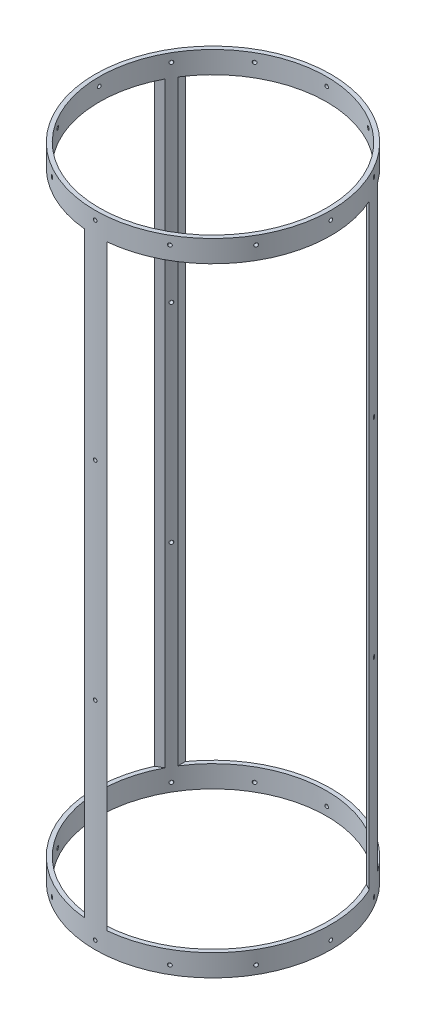
SolidWorks part; units mm, degrees
material "6061-T6 (SS)"
ref_plane "Front Plane" through (0, 0, 0) normal (0, 0, 1) x (1, 0, 0)
ref_plane "Top Plane" through (0, 0, 0) normal (0, 1, 0) x (1, 0, 0)
ref_plane "Right Plane" through (0, 0, 0) normal (1, 0, 0) x (0, 0, -1)
sketch "Sketch1" plane through (0, 0, 0) normal (0, 1, 0) x (1, 0, 0)
  circle A0 centre (0, 0) radius 88.9
  circle A1 centre (0, 0) radius 85.725
  dimension "D1" = 177.8
  dimension "D2" = 171.45
extrude "Boss-Extrude1" add sketch "Sketch1" along normal mid plane 482.854
sketch "Sketch2" plane through (0, 0, 0) normal (0, 0, 1) x (1, 0, 0)
  line L0 (85.725, 241.427) -> (-85.725, 241.427) construction
  line L1 (-72.39, -224.917) -> (72.39, -224.917)
  line L2 (-72.39, -224.917) -> (-72.39, 224.917)
  line L3 (-72.39, 224.917) -> (72.39, 224.917)
  line L4 (72.39, -224.917) -> (72.39, 224.917)
  line L5 (-72.39, -224.917) -> (72.39, 224.917) construction
  line L6 (-72.39, 224.917) -> (72.39, -224.917) construction
  line L7 (88.9, -241.427) -> (88.9, 241.427) construction
  point P0 (0, 0)
  dimension "D1" = 16.51
  dimension "D2" = 16.51
extrude "Cut-Extrude1" cut sketch "Sketch2" against normal up to surface (51.6033 mm away)
pattern_circular "CirPattern1" count 3 over 360 about axis through (0, 0, 0) along (0, 1, 0) of "Cut-Extrude1"
ref_plane "Plane1" through (88.9, 0, 0) normal (1, 0, 0) x (0, 0, -1)
sketch "Sketch4" plane through (88.9, 0, 0) normal (1, 0, 0) x (0, 0, -1)
  line L0 (0, 97.79) -> (0, -97.79) construction
  line L1 (88.9, 241.427) -> (-88.9, 241.427) construction
  circle A0 centre (0, 235.077) radius 1.3525
  dimension "D1" = 2.7051
  dimension "D2" = 6.35
extrude "Cut-Extrude3" cut sketch "Sketch4" against normal blind 15.24
pattern_circular "CirPattern3" count 12 over 360 about axis through (0, 241.427, 0) along (0, -1, 0) of "Cut-Extrude3"
mirror "Mirror1" about plane through (0, 0, 0) normal (0, 1, 0) of "Cut-Extrude3", "CirPattern3"
ref_plane "Plane2" through (0, 0, 88.9) normal (0, 0, 1) x (1, 0, 0)
sketch "Sketch5" plane through (0, 0, 88.9) normal (0, 0, 1) x (1, 0, 0)
  circle A0 centre (0, 78.359) radius 1.3526
  circle A1 centre (0, -78.359) radius 1.3526
  circle A2 centre (0, -235.077) radius 1.3525 construction
  circle A3 centre (0, 235.077) radius 1.3525 construction
  dimension "D1" = 156.718
  dimension "D2" = 156.718
  dimension "D3" = 2.7051
  dimension "D4" = 2.7051
extrude "Cut-Extrude4" cut sketch "Sketch5" against normal blind 22.86
pattern_circular "CirPattern4" count 3 over 360 about axis through (0, 241.427, 0) along (0, -1, 0) of "Cut-Extrude4"
